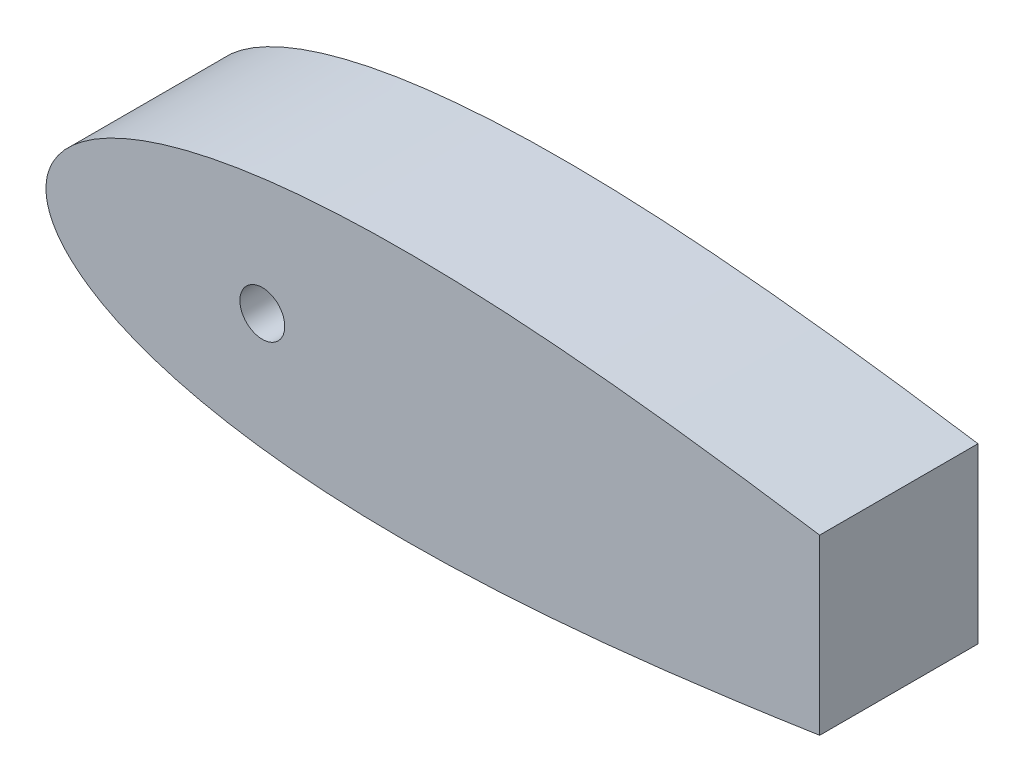
SolidWorks part; units mm, degrees
ref_plane "Front Plane" through (0, 0, 0) normal (0, 0, 1) x (1, 0, 0)
ref_plane "Top Plane" through (0, 0, 0) normal (0, 1, 0) x (1, 0, 0)
ref_plane "Right Plane" through (0, 0, 0) normal (1, 0, 0) x (0, 0, -1)
sketch "Sketch1" plane through (0, 0, 0) normal (0, 0, 1) x (1, 0, 0)
  line L0 (100, 0) -> (0, 0) construction
  line L1 (1.2169, -991.9959) -> (1.2169, 49008.0041) construction
  line L2 (93.345, 0) -> (114.935, 0) construction
  line L3 (125.634, 0) -> (131.6629, 0) construction
  line L4 (643.5991, 0) -> (643.5991, -1.016)
  line L9 (0, 0) -> (643.9668, 0)
  line L13 (460.661, 0) -> (473.361, 0)
  circle A0 centre (104.14, 0) radius 10.795 construction
  arc A1 (1.2169, -4.6585) -> (1.2169, 4.6585) centre (9.525, 0) cw
  arc A2 (641.5671, 0) -> (644.1071, 0) centre (642.8371, 0) ccw
  circle A4 centre (104.14, 0) radius 10.795
  circle A9 centre (40.64, 0) radius 12.7
  circle A14 centre (642.3793, 0) radius 1.5875 construction
  arc A15 (642.5108, -1.582) -> (642.5108, 1.582) centre (642.3793, 0) ccw
  spline S2 degree 3 poles (666.3448, -0.0547) (672.2538, 0) (666.3448, 0.0547) (662.8509, 0.2344) (656.505, 0.5436) (649.293, 1.0348) (640.4916, 1.7319) (630.4138, 2.6634) (619.0141, 3.8493) (606.375, 5.3044) (592.5439, 7.0376) (577.5855, 9.0506) (561.5643, 11.3389) (544.5497, 13.8907) (526.6141, 16.6877) (507.8326, 19.7051) (488.2827, 22.9117) (468.0444, 26.2704) (447.1994, 29.739) (425.8316, 33.2703) (404.0263, 36.8132) (381.8707, 40.3133) (359.4533, 43.7135) (336.8645, 46.9554) (314.1962, 49.9798) (291.5418, 52.7277) (268.9963, 55.1412) (246.6566, 57.1646) (224.6209, 58.7452) (202.9892, 59.8341) (181.8631, 60.3875) (161.3458, 60.367) (141.542, 59.7399) (122.5581, 58.4818) (104.5023, 56.5743) (87.485, 54.0089) (71.6197, 50.7848) (57.0237, 46.9125) (43.8205, 42.415) (32.1416, 37.3322) (22.1291, 31.7315) (13.9324, 25.7264) (7.6896, 19.5132) (3.4631, 13.4204) (1.1063, 7.9234) (0.1546, 3.5138) (-0.0622, 0) (0.1546, -3.5138) (1.1063, -7.9234) (3.4631, -13.4204) (7.6896, -19.5132) (13.9324, -25.7264) (22.1291, -31.7315) (32.1416, -37.3322) (43.8205, -42.415) (57.0237, -46.9125) (71.6197, -50.7848) (87.485, -54.0089) (104.5023, -56.5743) (122.5581, -58.4818) (141.542, -59.7399) (161.3458, -60.367) (181.8631, -60.3875) (202.9892, -59.8341) (224.6209, -58.7452) (246.6566, -57.1646) (268.9963, -55.1412) (291.5418, -52.7277) (314.1962, -49.9798) (336.8645, -46.9554) (359.4533, -43.7135) (381.8707, -40.3133) (404.0263, -36.8132) (425.8316, -33.2703) (447.1994, -29.739) (468.0444, -26.2704) (488.2827, -22.9117) (507.8326, -19.7051) (526.6141, -16.6877) (544.5497, -13.8907) (561.5643, -11.3389) (577.5855, -9.0506) (592.5439, -7.0376) (606.375, -5.3044) (619.0141, -3.8493) (630.4138, -2.6634) (640.4916, -1.7319) (649.293, -1.0348) (656.505, -0.5436) (662.8509, -0.2344) (666.3448, -0.0547) (672.2538, 0) (666.3448, 0.0547) knots -0.009667 -0.005395 -0.002168 0 0.002168 0.005395 0.009667 0.014967 0.021271 0.028553 0.036781 0.04592 0.055932 0.066773 0.078397 0.090755 0.103793 0.117456 0.131686 0.146422 0.1616 0.177156 0.193024 0.209135 0.225421 0.241812 0.258238 0.274629 0.290914 0.307025 0.322893 0.338448 0.353626 0.368361 0.38259 0.396253 0.40929 0.421647 0.43327 0.444109 0.454119 0.463255 0.471479 0.478755 0.485052 0.490344 0.49461 0.497833 0.5 0.502167 0.50539 0.509656 0.514948 0.521245 0.528521 0.536745 0.545881 0.555891 0.56673 0.578353 0.59071 0.603747 0.61741 0.631639 0.646374 0.661552 0.677107 0.692975 0.709086 0.725371 0.741762 0.758188 0.774579 0.790865 0.806976 0.822844 0.8384 0.853578 0.868314 0.882544 0.896207 0.909245 0.921603 0.933227 0.944068 0.95408 0.963219 0.971447 0.978729 0.985033 0.990333 0.994605 0.997832 1 1.002168 1.005395 1.009667 only from (670.56, 0) to (670.56, 0)
  point P2 (167.64, 0)
  point P8 (1.2169, -4.6585)
  point P10 (1.2169, 4.6585)
  point P28 (133.9182, 0)
  point P49 (130.0977, 0)
  point P59 (95.1064, 0)
  dimension "D2" = 21.59
  dimension "D3" = 1.016
  dimension "D4" = 1.27
  dimension "D8" = 25.4
  dimension "D9" = 63.5
  dimension "D10" = 3.175
  dimension "D6" = 63.5
extrude "Boss-Extrude1" add sketch "Sketch1" along normal blind 76.2 contours S2
sketch "Sketch3" plane through (0, 0, 76.2) normal (0, 0, 1) x (1, 0, 0)
  circle A0 centre (104.1392, 0) radius 10.795
  dimension "D1" = 21.59
extrude "Cut-Extrude2" cut sketch "Sketch3" against normal blind 76.2
sketch "Sketch4" plane through (0, 0, 76.2) normal (0, 0, 1) x (1, 0, 0)
sketch "Sketch6" plane through (0, 0, 0) normal (1, 0, 0) x (0, 0, -1)
  circle A0 centre (-20.32, 0) radius 6.35
  dimension "D1" = 12.7
  dimension "D2" = 20.32
extrude "Cut-Extrude3" cut sketch "Sketch6" against normal blind 0.0003 and the other way blind 53.34
sketch "Sketch7" plane through (0, 0, 0) normal (0, 0, -1) x (-1, 0, 0)
  circle A0 centre (-38.1, 0) radius 1.5875
  circle A1 centre (-50.8, 0) radius 1.5875
  point P4 (0, 0)
  dimension "D1" = 3.175
  dimension "D2" = 3.175
  dimension "D3" = 12.7
  dimension "D4" = 38.1
extrude "Cut-Extrude4" cut sketch "Sketch7" against normal blind 30.48
sketch "Sketch8" plane through (0, 0, 0) normal (0, 0, -1) x (-1, 0, 0)
  line L1 (-677.2433, 63.9901) -> (-372.4433, 63.9901)
  line L2 (-677.2433, 63.9901) -> (-677.2433, -63.0099)
  line L3 (-677.2433, -63.0099) -> (-372.4433, -63.0099)
  line L4 (-372.4433, 63.9901) -> (-372.4433, -63.0099)
  dimension "D1" = 127
  dimension "D2" = 372.4433
  dimension "D3" = 304.8
extrude "Cut-Extrude5" cut sketch "Sketch8" against normal blind 76.2
